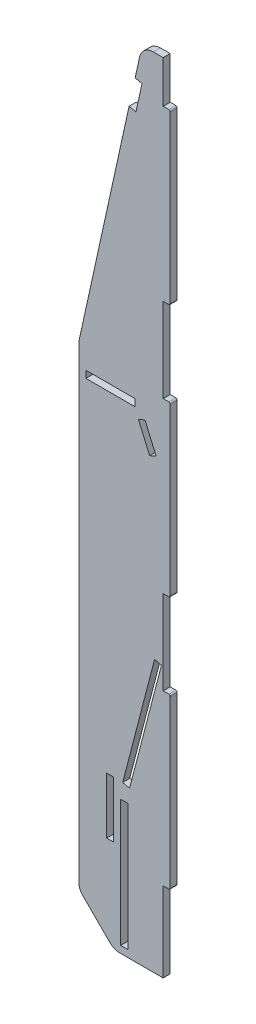
SolidWorks part; units mm, degrees
ref_plane "Front" through (0, 0, 0) normal (0, 0, 1) x (1, 0, 0)
ref_plane "Top" through (0, 0, 0) normal (0, 1, 0) x (1, 0, 0)
ref_plane "Right" through (0, 0, 0) normal (1, 0, 0) x (0, 0, -1)
sketch "Sketch1" plane through (0, 0, 0) normal (0, 0, 1) x (1, 0, 0)
  line L0 (80, 33.22) -> (20, 33.22)
  line L3 (20, 600) -> (80, 600)
  line L4 (80, 33.22) -> (80, 89.95)
  line L5 (20, 600) -> (20, 33.22)
  line L6 (80, 570.05) -> (80, 600)
  line L7 (80, 89.95) -> (85, 89.95)
  line L9 (80, 210.05) -> (85, 210.05)
  line L10 (85, 89.95) -> (85, 210.05)
  line L11 (80, 269.95) -> (85, 269.95)
  line L13 (80, 390.05) -> (85, 390.05)
  line L14 (85, 269.95) -> (85, 390.05)
  line L15 (80, 570.05) -> (85, 570.05)
  line L17 (80, 449.95) -> (85, 449.95)
  line L18 (85, 570.05) -> (85, 449.95)
  line L19 (80, 390.05) -> (80, 449.95)
  line L20 (80, 210.05) -> (80, 269.95)
  dimension "D1" = 600
  dimension "D2" = 120.1
  dimension "D3" = 33.22
  dimension "D4" = 20
  dimension "D5" = 60
  dimension "D6" = 120.1
  dimension "D7" = 120.1
  dimension "D8" = 5
  dimension "D9" = 5
  dimension "D10" = 5
  dimension "D11" = 29.95
  dimension "D12" = 59.9
  dimension "D13" = 59.9
extrude "Boss-Extrude1" add sketch "Sketch1" along normal blind 5
sketch "Sketch2" plane through (0, 0, 5) normal (0, 0, 1) x (1, 0, 0)
  line L0 (80, 600) -> (20, 600) construction
  line L1 (25, 380) -> (65, 380) construction
  line L2 (25, 380) -> (25, 375) construction
  line L3 (25, 375) -> (65, 375) construction
  line L4 (65, 380) -> (65, 375) construction
  line L5 (80, 33.22) -> (80, 89.95) construction
  line L6 (65, 375) -> (77, 347.5045) construction
  line L7 (77, 347.5045) -> (72.4174, 345.5045) construction
  line L8 (72.4174, 345.5045) -> (60.4174, 373) construction
  line L9 (60.4174, 373) -> (65, 375) construction
  line L10 (67, 370.4174) -> (62.4174, 368.4174)
  line L11 (62.4174, 368.4174) -> (70.4174, 350.0871)
  line L12 (70.4174, 350.0871) -> (75, 352.0871)
  line L13 (75, 352.0871) -> (67, 370.4174)
  line L14 (80, 230) -> (75.1609, 231.258) construction
  line L15 (75.1609, 231.258) -> (50, 134.4751) construction
  line L16 (50, 134.4751) -> (54.8391, 133.2171) construction
  line L17 (54.8391, 133.2171) -> (80, 230) construction
  line L18 (73.9028, 226.4189) -> (51.258, 139.3143)
  line L19 (73.9028, 226.4189) -> (78.742, 225.1609)
  line L20 (51.258, 139.3143) -> (56.0972, 138.0562)
  line L21 (78.742, 225.1609) -> (56.0972, 138.0562)
  line L23 (54.8391, 133.2171) -> (49.8391, 133.2171) construction
  line L24 (54.8391, 133.2171) -> (54.8391, 33.2171) construction
  line L25 (54.8391, 33.2171) -> (49.8391, 33.2171) construction
  line L26 (49.8391, 133.2171) -> (49.8391, 33.2171) construction
  line L27 (49.8391, 128.2171) -> (54.8391, 128.2171)
  line L28 (49.8391, 128.2171) -> (49.8391, 38.2171)
  line L29 (49.8391, 38.2171) -> (54.8391, 38.2171)
  line L30 (54.8391, 128.2171) -> (54.8391, 38.2171)
  line L31 (39.8391, 139.3143) -> (44.8391, 139.3143)
  line L32 (39.8391, 139.3143) -> (39.8391, 99.3143)
  line L33 (39.8391, 99.3143) -> (44.8391, 99.3143)
  line L34 (44.8391, 139.3143) -> (44.8391, 99.3143)
  line L35 (60, 380) -> (25, 380)
  line L36 (60, 380) -> (60, 375)
  line L37 (60, 375) -> (25, 375)
  line L38 (25, 380) -> (25, 375)
  point P30 (52.3391, 33.2171)
  dimension "D1" = 220
  dimension "D2" = 5
  dimension "D3" = 5
  dimension "D4" = 15
  dimension "D5" = 5
  dimension "D6" = 20
  dimension "D7" = 3
  dimension "D8" = 30
  dimension "D9" = 5
  dimension "D10" = 5
  dimension "D11" = 370
  dimension "D12" = 30
  dimension "D13" = 100
  dimension "D14" = 5
  dimension "D15" = 5
  dimension "D16" = 5
  dimension "D17" = 100
  dimension "D18" = 5
  dimension "D19" = 5
  dimension "D20" = 5
  dimension "D21" = 5
  dimension "D22" = 40
  dimension "D23" = 35
extrude "Cut-Extrude1" cut sketch "Sketch2" against normal blind 10
sketch "Sketch3" plane through (0, 0, 5) normal (0, 0, 1) x (1, 0, 0)
  line L0 (20, 395) -> (65, 600)
  line L1 (20, 600) -> (20, 33.22) construction
  line L2 (80, 600) -> (20, 600) construction
  line L4 (20, 395) -> (1.5136, 616.0876)
  line L5 (1.5136, 616.0876) -> (65, 600)
  line L6 (45, 33.22) -> (20, 58.22)
  line L7 (20, 33.22) -> (80, 33.22) construction
  line L8 (20, 58.22) -> (13.4525, 20.5561)
  line L9 (13.4525, 20.5561) -> (45, 33.22)
  line L10 (60, 380) -> (25, 380) construction
  dimension "D1" = 15
  dimension "D2" = 15
  dimension "D3" = 25
  dimension "D4" = 25
extrude "Cut-Extrude2" cut sketch "Sketch3" against normal blind 10
fillet "Fillet1" radius 1 6 edges at (85, 570.05, 2.5) (85, 449.95, 2.5) (85, 390.05, 2.5) (85, 269.95, 2.5) (85, 210.05, 2.5) (85, 89.95, 2.5)
fillet "Fillet2" radius 10 4 edges at (65, 600, 2.5) (20, 395, 2.5) (20, 58.22, 2.5) (45, 33.22, 2.5)
sketch "Sketch4" plane through (0, 0, 5) normal (0, 0, 1) x (1, 0, 0)
  line L0 (61.1315, 582.3766) -> (66.0152, 581.3046) construction
  line L1 (61.1315, 582.3766) -> (54.6992, 553.0743) construction
  line L2 (66.0152, 581.3046) -> (59.583, 552.0023) construction
  line L3 (54.6992, 553.0743) -> (59.583, 552.0023) construction
  line L4 (60.0594, 577.4929) -> (64.9431, 576.4209)
  line L5 (60.0594, 577.4929) -> (55.7713, 557.958)
  line L6 (64.9431, 576.4209) -> (60.655, 556.886)
  line L7 (55.7713, 557.958) -> (60.655, 556.886)
  dimension "D1" = 30
  dimension "D2" = 5
  dimension "D3" = 20
  dimension "D4" = 5
  dimension "D5" = 10
extrude "Cut-Extrude3" cut sketch "Sketch4" against normal blind 10
